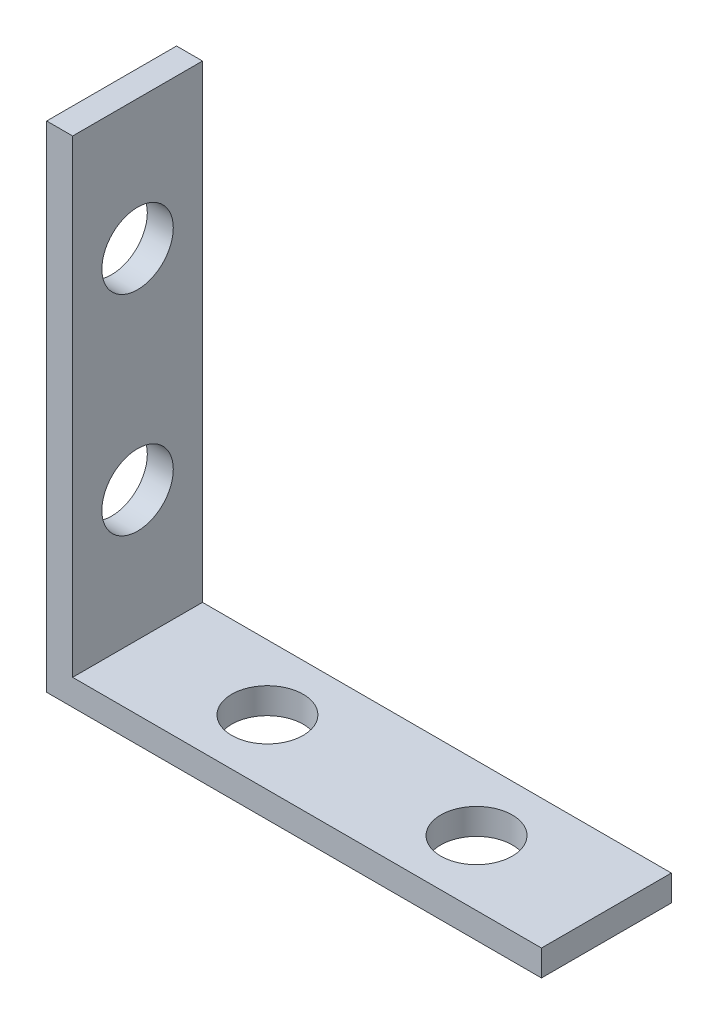
SolidWorks part; units mm, degrees
ref_plane "Front Plane" through (0, 0, 0) normal (0, 0, 1) x (1, 0, 0)
ref_plane "Top Plane" through (0, 0, 0) normal (0, 1, 0) x (1, 0, 0)
ref_plane "Right Plane" through (0, 0, 0) normal (1, 0, 0) x (0, 0, -1)
sketch "Sketch1" plane through (0, 0, 0) normal (0, 0, 1) x (1, 0, 0)
  line L0 (0, 0) -> (38.1, 0)
  line L1 (38.1, 0) -> (38.1, 2)
  line L2 (38.1, 2) -> (2, 2)
  line L3 (2, 2) -> (2, 38.1)
  line L4 (2, 38.1) -> (0, 38.1)
  line L5 (0, 38.1) -> (0, 0)
  dimension "D1" = 2
  dimension "D2" = 2
  dimension "D3" = 38.1
  dimension "D4" = 38.1
extrude "Boss-Extrude1" add sketch "Sketch1" along normal blind 10
hole_wizard "M5 Clearance Hole4" positions "3DSketch1" profile "Sketch3" hole size "M5" standard "ANSI Metric" end condition through all
sketch3d "3DSketch1"
  line L0 (2, 2, 10) -> (2, 2, 0) construction
  line L1 (2, 38.1, 10) -> (2, 38.1, 0) construction
  point P0 (2, 12, 5)
  point P2 (2, 28.1, 5)
  point P4 (12, 2, 5)
  point P6 (28.1, 2, 5)
  dimension "D1" = 5
  dimension "D2" = 10
  dimension "D3" = 10
  dimension "D4" = 5
  dimension "D5" = 10
  dimension "D6" = 10
sketch "Sketch3" plane through (2, 12, 5) normal (0, 1, 0) x (0, 0, -1)
  line L0 (0, 0) -> (0, 2)
  line L1 (0, 2) -> (2.75, 2)
  line L2 (2.75, 2) -> (2.75, 0)
  line L5 (2.75, 0) -> (0, 0)
  line L11 (0, -6.35) -> (0, 107.95) construction
  dimension "Thru Hole Dia." = 5.5
  dimension "Thru Hole Depth" = 2
